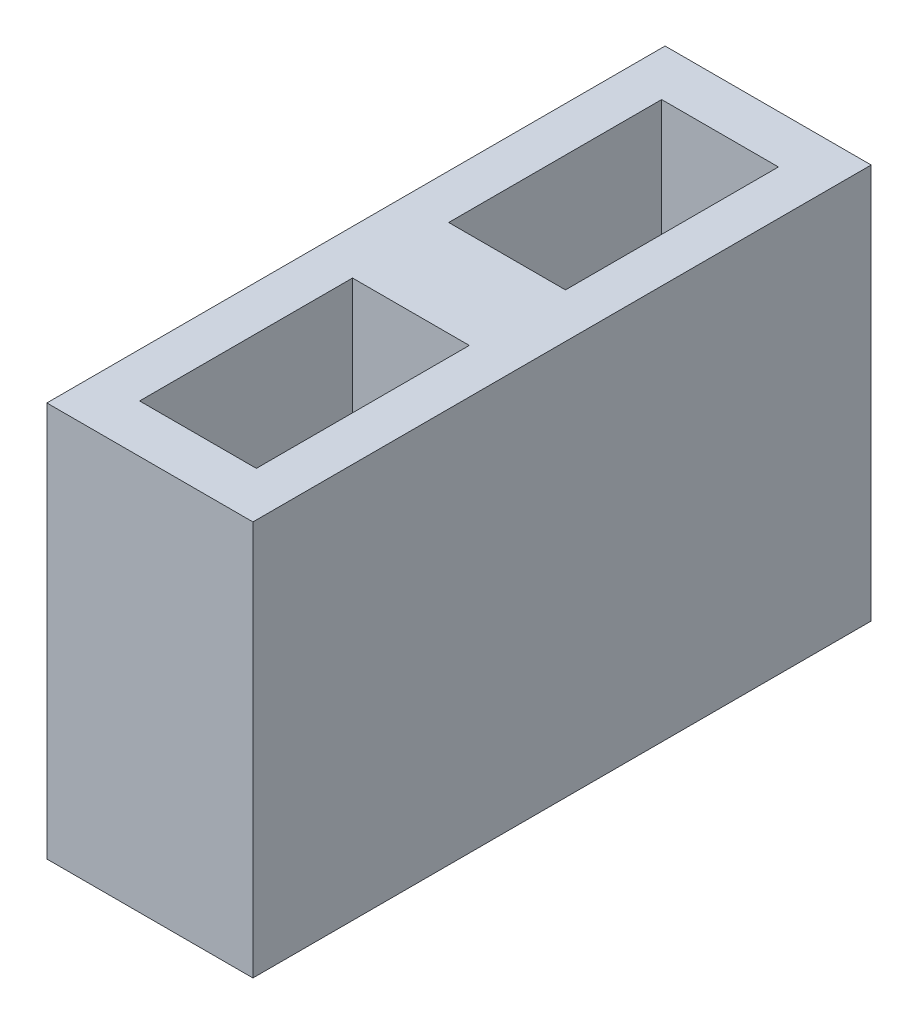
SolidWorks part; units mm, degrees
ref_plane "Front Plane" through (0, 0, 0) normal (0, 0, 1) x (1, 0, 0)
ref_plane "Top Plane" through (0, 0, 0) normal (0, 1, 0) x (1, 0, 0)
ref_plane "Right Plane" through (0, 0, 0) normal (1, 0, 0) x (0, 0, -1)
sketch "Sketch1" plane through (0, 0, 0) normal (0, 1, 0) x (1, 0, 0)
  line L0 (-3, 3) -> (-3, 9)
  line L1 (-3, 9) -> (3, 9)
  line L2 (3, 9) -> (3, 3)
  line L3 (3, 3) -> (9, 3)
  line L4 (9, 3) -> (9, -3)
  line L5 (9, -3) -> (3, -3)
  line L6 (3, -3) -> (3, -9)
  line L7 (3, -9) -> (-3, -9)
  line L8 (-3, -9) -> (-3, -3)
  line L9 (-3, -3) -> (-9, -3)
  line L10 (-9, -3) -> (-9, 3)
  line L11 (-9, 3) -> (-3, 3)
  point P13 (-9, 0)
  point P14 (0, 9)
  dimension "D1" = 6
  dimension "D2" = 6
extrude "Boss-Extrude1" add sketch "Sketch1" along normal blind 1.5
sketch "Sketch3" plane through (0, 1.5, 0) normal (0, 1, 0) x (1, 0, 0)
  line L0 (-1.7, 1.7) -> (-7.6, 1.7)
  line L1 (-7.6, 1.7) -> (-7.6, -1.7)
  line L2 (-7.6, -1.7) -> (-1.7, -1.7)
  line L3 (-1.7, -1.7) -> (-1.7, -7.6)
  line L4 (-1.7, -7.6) -> (1.7, -7.6)
  line L5 (1.7, -7.6) -> (1.7, -1.7)
  line L6 (1.7, -1.7) -> (7.6, -1.7)
  line L7 (7.6, -1.7) -> (7.6, 1.7)
  line L8 (7.6, 1.7) -> (1.7, 1.7)
  line L9 (1.7, 1.7) -> (1.7, 7.6)
  line L10 (1.7, 7.6) -> (-1.7, 7.6)
  line L11 (-1.7, 7.6) -> (-1.7, 1.7)
  line L12 (-3, 3) -> (-9, 3)
  line L13 (-9, 3) -> (-9, -3)
  line L14 (-9, -3) -> (-3, -3)
  line L15 (-3, -3) -> (-3, -9)
  line L16 (-3, -9) -> (3, -9)
  line L17 (3, -9) -> (3, -3)
  line L18 (3, -3) -> (9, -3)
  line L19 (9, -3) -> (9, 3)
  line L20 (9, 3) -> (3, 3)
  line L21 (3, 3) -> (3, 9)
  line L22 (3, 9) -> (-3, 9)
  line L23 (-3, 9) -> (-3, 3)
  line L24 (-3, 3) -> (-9, 3)
  line L25 (-9, 3) -> (-9, -3)
  line L26 (-9, -3) -> (-3, -3)
  line L27 (-3, -3) -> (-3, -9)
  line L28 (-3, -9) -> (3, -9)
  line L29 (3, -9) -> (3, -3)
  line L30 (3, -3) -> (9, -3)
  line L31 (9, -3) -> (9, 3)
  line L32 (9, 3) -> (3, 3)
  line L33 (3, 3) -> (3, 9)
  line L34 (3, 9) -> (-3, 9)
  line L35 (-3, 9) -> (-3, 3)
  line L36 (9, -3) -> (9, 3) construction
  point P24 (0, 7.6)
  point P25 (-7.6, 0)
  point P26 (0, -7.6)
  point P27 (7.6, 0)
  dimension "D2" = 1.3
  dimension "D3" = 1.3
  dimension "D4" = 1.4
  dimension "D5" = 1.4
  dimension "D6" = 1.4
  dimension "D7" = 1.4
extrude "Boss-Extrude5" add sketch "Sketch3" along normal blind 10
sketch "Sketch2" plane through (0, 1.5, 0) normal (0, 1, 0) x (1, 0, 0)
  line L1 (-1.4, 1.4) -> (1.4, 1.4)
  line L2 (-1.4, 1.4) -> (-1.4, -1.4)
  line L3 (-1.4, -1.4) -> (1.4, -1.4)
  line L4 (1.4, 1.4) -> (1.4, -1.4)
  point P4 (-1.4, 0)
  point P5 (0, 1.4)
  dimension "D1" = 2.8
extrude "Boss-Extrude2" add sketch "Sketch2" along normal blind 10
sketch "Sketch4" plane through (0, 11.5, 0) normal (0, 1, 0) x (1, 0, 0)
  line L1 (-9, 3) -> (-3, 3)
  line L2 (-9, 3) -> (-9, -3)
  line L3 (-9, -3) -> (-3, -3)
  line L4 (-3, 3) -> (-3, -3)
extrude "Cut-Extrude1" cut sketch "Sketch4" against normal through all
sketch "Sketch5" plane through (0, 11.5, 0) normal (0, 1, 0) x (1, 0, 0)
  line L0 (-1.4, 1.4) -> (-1.4, -1.4) construction
  line L1 (-3, 1.7) -> (-1.7, 1.7)
  line L2 (-3, 1.7) -> (-3, -1.7)
  line L3 (-3, -1.7) -> (-1.7, -1.7)
  line L4 (-1.7, 1.7) -> (-1.7, 1.4)
  line L5 (-1.4, 1.4) -> (-1.7, 1.4)
  line L6 (-1.4, 1.4) -> (-1.4, -1.4)
  line L7 (-1.4, -1.4) -> (-1.7, -1.4)
  line L9 (1.4, 1.4) -> (-1.4, 1.4) construction
  line L10 (-1.4, -1.4) -> (1.4, -1.4) construction
  line L11 (-1.7, -1.4) -> (-1.7, -1.7)
extrude "Boss-Extrude6" add sketch "Sketch5" against normal blind 10
sketch "Sketch6" [suppressed] plane through (0, 11.5, 0) normal (0, 1, 0) x (1, 0, 0)
  line L1 (-3, 9) -> (3, 9)
  line L2 (-3, 9) -> (-3, 3)
  line L3 (-3, 3) -> (3, 3)
  line L4 (3, 9) -> (3, 3)
extrude "Cut-Extrude2" [suppressed] cut sketch "Sketch6" against normal through all
sketch "Sketch7" [suppressed] plane through (0, 11.5, 0) normal (0, 1, 0) x (1, 0, 0)
  line L0 (1.4, 1.4) -> (-1.7, 1.4) construction
  line L1 (-1.7, 3) -> (-1.7, 1.4) construction
  line L2 (-1.7, 3) -> (1.7, 3) construction
  line L3 (1.4, 1.4) -> (-1.7, 1.4)
  line L4 (-1.7, 3) -> (-1.7, 1.4)
  line L5 (-1.7, 3) -> (1.7, 3)
  line L8 (1.7, 3) -> (1.7, 1.7)
  line L9 (1.7, 1.7) -> (1.4, 1.7)
  line L10 (1.4, 1.7) -> (1.4, 1.4)
extrude "Boss-Extrude7" [suppressed] add sketch "Sketch7" against normal blind 10
sketch "Sketch8" plane through (0, 11.5, 0) normal (0, 1, 0) x (1, 0, 0)
  line L1 (3, 3) -> (9, 3)
  line L2 (3, 3) -> (3, -3)
  line L3 (3, -3) -> (9, -3)
  line L4 (9, 3) -> (9, -3)
extrude "Cut-Extrude3" cut sketch "Sketch8" against normal through all
sketch "Sketch9" plane through (0, 11.5, 0) normal (0, 1, 0) x (1, 0, 0)
  line L0 (1.4, -1.4) -> (1.4, 1.4) construction
  line L1 (3, 1.7) -> (1.7, 1.7) construction
  line L2 (3, 1.7) -> (3, -1.7) construction
  line L3 (1.7, -1.7) -> (3, -1.7) construction
  line L4 (1.4, -1.4) -> (1.4, 1.4)
  line L5 (3, 1.7) -> (1.7, 1.7)
  line L6 (3, 1.7) -> (3, -1.7)
  line L7 (1.7, -1.7) -> (3, -1.7)
  line L8 (1.4, 1.4) -> (1.7, 1.4)
  line L9 (1.7, 1.4) -> (1.7, 1.7)
  line L10 (1.4, -1.4) -> (1.7, -1.4)
  line L11 (1.7, -1.4) -> (1.7, -1.7)
extrude "Boss-Extrude8" add sketch "Sketch9" against normal blind 10
sketch "Sketch10" plane through (0, 11.5, 0) normal (0, 1, 0) x (1, 0, 0)
  line L4 (-3, 9) -> (-3, -9)
  line L20 (-3, 9) -> (-3, -9)
  line L30 (3, 9) -> (-3, 9)
  line L32 (3, 9) -> (-3, 9)
  line L33 (-3, -9) -> (3, -9)
  line L34 (-3, -9) -> (3, -9)
  line L35 (3, -9) -> (3, 9)
  line L36 (3, -9) -> (3, 9)
  dimension "D1" = 0
extrude "Boss-Extrude9" [suppressed] add sketch "Sketch10" along normal blind 40
sketch "Sketch11" plane through (0, 11.5, 0) normal (0, 1, 0) x (1, 0, 0)
  line L0 (-3, 9) -> (-3, -9) construction
  line L5 (1.7, 1.4) -> (-3, 1.4)
  line L6 (1.7, 1.4) -> (1.7, -1.4)
  line L7 (1.7, -1.4) -> (-3, -1.4)
  line L8 (-3, 1.4) -> (-3, -1.4)
  line L9 (-1.7, -1.4) -> (1.7, -1.4) construction
extrude "Boss-Extrude10" [suppressed] add sketch "Sketch11" along normal blind 40
sketch "Sketch12" [suppressed] plane through (0, 11.5, 0) normal (0, 1, 0) x (1, 0, 0)
  line L0 (-1.6, -1.45) -> (1.45, -1.45) construction
  line L1 (1.45, -1.45) -> (-3, -1.45)
  line L2 (1.45, -1.45) -> (1.45, 3)
  line L3 (1.45, 3) -> (-3, 3)
  line L4 (-3, -1.45) -> (-3, 3)
  line L5 (1.45, -1.45) -> (1.45, 1.6) construction
extrude "Boss-Extrude11" [suppressed] add sketch "Sketch12" along normal blind 40
sketch "Sketch13" [suppressed] plane through (0, 11.5, 0) normal (0, 1, 0) x (1, 0, 0)
  line L0 (-3, 9) -> (-3, -9) construction
  line L1 (-3, 1.435) -> (3, 1.435)
  line L2 (-3, 1.435) -> (-3, -1.435)
  line L3 (-3, -1.435) -> (3, -1.435)
  line L4 (3, 1.435) -> (3, -1.435)
  line L5 (3, -9) -> (3, 9) construction
  line L7 (1.63, 1.435) -> (-1.63, 1.435) construction
  line L8 (-1.63, -1.435) -> (1.63, -1.435) construction
extrude "Boss-Extrude12" [suppressed] add sketch "Sketch13" along normal blind 40
equation "\"mdfWidth\"= 3"
equation "\"cellSide\"= 180"
equation "\"mazeHeight\"= 50"
equation "\"slitHeight\"= 10"
equation "\"gripWidth\"= 6"
equation "\"wallThickness\"= 1.5"
equation "\"slitWidth\"= \"wallThickness\""
equation "\"D1@Sketch1\"= \"mdfWidth\" + 2 * \"wallThickness\""
equation "\"D2@Sketch1\"=\"gripWidth\""
equation "\"D1@Boss-Extrude1\"= \"wallThickness\""
equation "\"D1@Boss-Extrude2\"= \"slitHeight\""
equation "\"D2@Sketch3\"=\"wallThickness\" - \"playSides\""
equation "\"D1@Boss-Extrude5\"= \"slitHeight\""
equation "\"jeu\"= 0.13"
equation "\"D1@Sketch2\"=\"mdfWidth\"- 2* \"playEnds\""
equation "\"D1@Boss-Extrude6\"= \"slitHeight\""
equation "\"D1@Boss-Extrude7\"= \"slitHeight\""
equation "\"D1@Boss-Extrude8\"= \"slitHeight\""
equation "\"D1@Boss-Extrude9\"= \"mazeHeight\" - \"slitHeight\""
equation "\"D1@Boss-Extrude10\"= \"mazeHeight\" - \"slitHeight\""
equation "\"D1@Boss-Extrude11\"= \"mazeHeight\" - \"slitHeight\""
equation "\"D1@Boss-Extrude12\"= \"mazeHeight\" - \"slitHeight\""
equation "\"playEnds\"= 0.1"
equation "\"playSides\"= 0.2"
equation "\"D3@Sketch3\"=\"D2@Sketch3\""
equation "\"D4@Sketch3\"= \"wallThickness\" - \"playEnds\""
equation "\"D5@Sketch3\"= \"D4@Sketch3\""
equation "\"D6@Sketch3\"=\"D4@Sketch3\""
equation "\"D7@Sketch3\"= \"D4@Sketch3\""
